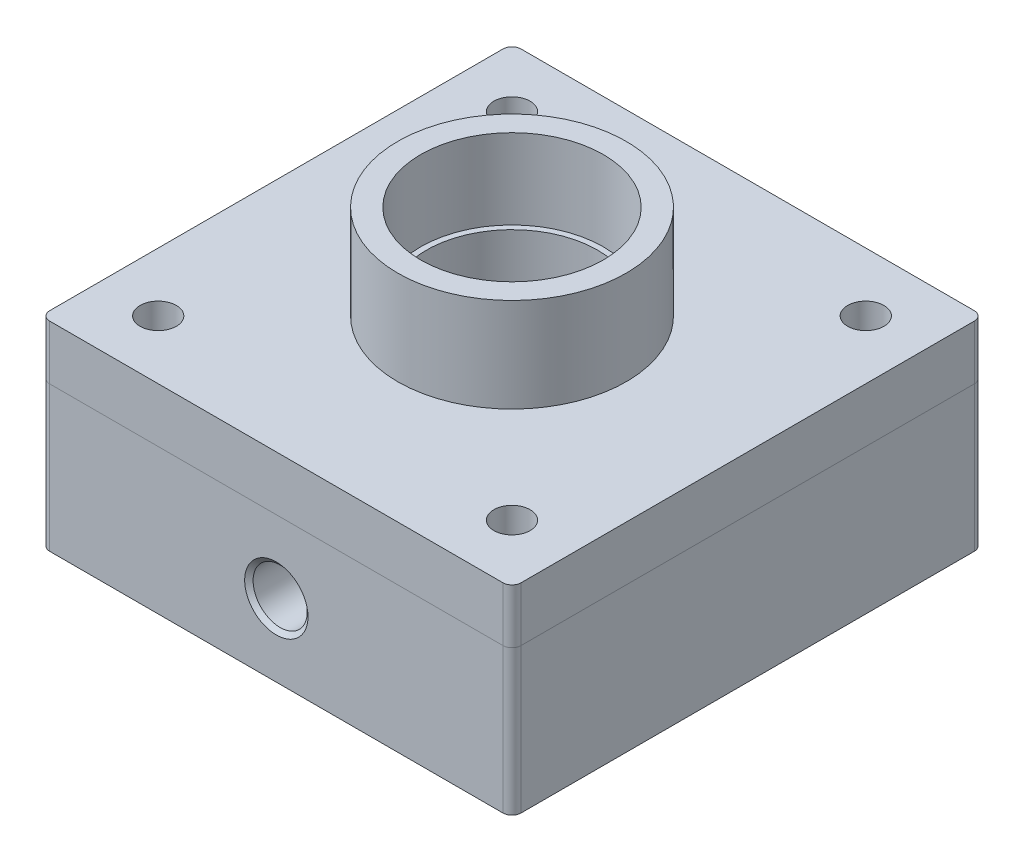
SolidWorks part; units mm, degrees
ref_plane "Front Plane" through (0, 0, 0) normal (0, 0, 1) x (1, 0, 0)
ref_plane "Top Plane" through (0, 0, 0) normal (0, 1, 0) x (1, 0, 0)
ref_plane "Right Plane" through (0, 0, 0) normal (1, 0, 0) x (0, 0, -1)
sketch "Sketch1" plane through (0, 0, 0) normal (0, 1, 0) x (1, 0, 0)
  line L1 (-82.55, 82.55) -> (82.55, 82.55)
  line L2 (-82.55, 82.55) -> (-82.55, -82.55)
  line L3 (-82.55, -82.55) -> (82.55, -82.55)
  line L4 (82.55, 82.55) -> (82.55, -82.55)
  line L5 (-82.55, 82.55) -> (82.55, -82.55) construction
  line L6 (-82.55, -82.55) -> (82.55, 82.55) construction
  point P0 (0, 0)
  dimension "D1" = 165.1
extrude "Boss-Extrude1" add sketch "Sketch1" along normal blind 50.8
sketch "Sketch2" plane through (0, 50.8, 0) normal (0, 1, 0) x (1, 0, 0)
  circle A0 centre (0, 0) radius 40
  dimension "D1" = 80
extrude "Boss-Extrude2" add sketch "Sketch2" along normal blind 52
sketch "Sketch3" plane through (0, 102.8, 0) normal (0, 1, 0) x (1, 0, 0)
  circle A0 centre (0, 0) radius 32
  dimension "D1" = 64
extrude "Cut-Extrude1" cut sketch "Sketch3" against normal blind 28
sketch "Sketch4" plane through (0, 74.8, 0) normal (0, 1, 0) x (1, 0, 0)
  circle A0 centre (0, 0) radius 30
  dimension "D1" = 60
extrude "Cut-Extrude2" cut sketch "Sketch4" against normal blind 22
fillet "Fillet1" radius 3.175 4 edges at (-82.55, 25.4, 82.55) (-82.55, 25.4, -82.55) (82.55, 25.4, -82.55) (82.55, 25.4, 82.55)
sketch "Sketch5" plane through (0, 0, 0) normal (0, -1, 0) x (1, 0, 0)
  circle A0 centre (0, 0) radius 20
  dimension "D1" = 40
extrude "Cut-Extrude3" cut sketch "Sketch5" against normal blind 40
sketch "Sketch6" plane through (0, 0, 0) normal (0, -1, 0) x (1, 0, 0)
  circle A0 centre (0, 0) radius 76.2
  circle A1 centre (0, 0) radius 69.85
  dimension "D1" = 152.4
  dimension "D2" = 139.7
extrude "Cut-Extrude4" cut sketch "Sketch6" against normal blind 8
sketch "Sketch7" plane through (0, 0, 82.55) normal (0, 0, 1) x (1, 0, 0)
  line L0 (-79.375, 25.4) -> (79.375, 25.4) construction
  line L1 (-79.375, 50.8) -> (-79.375, 0) construction
  line L2 (79.375, 0) -> (79.375, 50.8) construction
hole_wizard "1/2-14 NPSM Tapped Hole1" positions "Sketch8" profile "Sketch9" tap size "1/2-14 NPSM" standard "ANSI Inch"
sketch "Sketch8" plane through (0, 0, 82.55) normal (0, 0, 1) x (1, 0, 0)
  line L0 (-79.375, 25.4) -> (79.375, 25.4) construction
  point P0 (0, 25.4)
sketch "Sketch9" plane through (0, 25.4, 82.55) normal (1, 0, 0) x (0, -1, 0)
  line L0 (0, 0) -> (0, 52.9403)
  line L1 (0, 52.9403) -> (9.4869, 47.24)
  line L2 (9.4869, 47.24) -> (9.4869, 1.3427)
  line L3 (9.4869, 1.3427) -> (11.0871, 0)
  line L5 (11.0871, 0) -> (0, 0)
  line L6 (-9.4869, 1.3427) -> (-11.0871, 0) construction
  line L10 (0, 52.9403) -> (-9.4869, 47.24) construction
  line L11 (0, -6.35) -> (0, 107.95) construction
  dimension "Tap Drill Dia." = 18.9738
  dimension "Tap Drill Depth" = 47.24
  dimension "Near C'Sink Dia." = 22.1742
  dimension "Near C'Sink Angle" = 100
  dimension "Drill Angle" = 118
cosmetic thread "Hole Thread1" parameters "D1"=41.91, "D2"=20.9042
sketch "Sketch10" plane through (0, 0, 0) normal (0, -1, 0) x (1, 0, 0)
  line L0 (-79.375, 82.55) -> (79.375, 82.55) construction
  circle A0 centre (0, 50.55) radius 6.35
  dimension "D2" = 12.7
  dimension "D1" = 32
extrude "Cut-Extrude5" cut sketch "Sketch10" against normal blind 25
sketch "Sketch11" plane through (0, 0, 0) normal (0, -1, 0) x (1, 0, 0)
  line L1 (-61.9638, 61.9638) -> (61.9638, 61.9638) construction
  line L2 (-61.9638, 61.9638) -> (-61.9638, -61.9638) construction
  line L3 (-61.9638, -61.9638) -> (61.9638, -61.9638) construction
  line L4 (61.9638, 61.9638) -> (61.9638, -61.9638) construction
  line L5 (-61.9638, 61.9638) -> (61.9638, -61.9638) construction
  line L6 (-61.9638, -61.9638) -> (61.9638, 61.9638) construction
  circle A0 centre (0, 0) radius 87.63 construction
  circle A1 centre (-61.9638, 61.9638) radius 6.35
  circle A2 centre (61.9638, 61.9638) radius 6.35
  circle A3 centre (61.9638, -61.9638) radius 6.35
  circle A4 centre (-61.9638, -61.9638) radius 6.35
  dimension "D1" = 175.26
  dimension "D2" = 12.7
extrude "Cut-Extrude6" cut sketch "Sketch11" against normal through all
sketch "Sketch13" plane through (0, 50.8, 0) normal (0, 1, 0) x (1, 0, 0)
  line L4 (-82.55, 79.375) -> (-82.55, -79.375)
  line L5 (-79.375, -82.55) -> (79.375, -82.55)
  line L6 (82.55, -79.375) -> (82.55, 79.375)
  line L7 (79.375, 82.55) -> (-79.375, 82.55)
  line L8 (-82.55, 79.375) -> (-82.55, -79.375)
  line L9 (-79.375, -82.55) -> (79.375, -82.55)
  line L10 (82.55, -79.375) -> (82.55, 79.375)
  line L11 (79.375, 82.55) -> (-79.375, 82.55)
  circle A0 centre (61.9638, 61.9638) radius 6.35 construction
  circle A1 centre (61.9638, -61.9638) radius 6.35 construction
  circle A2 centre (0, 0) radius 40 construction
  circle A3 centre (-61.9638, -61.9638) radius 6.35 construction
  circle A4 centre (-61.9638, 61.9638) radius 6.35 construction
  circle A5 centre (61.9638, 61.9638) radius 6.35
  circle A6 centre (61.9638, -61.9638) radius 6.35
  circle A7 centre (0, 0) radius 40
  circle A8 centre (-61.9638, -61.9638) radius 6.35
  circle A9 centre (-61.9638, 61.9638) radius 6.35
  arc A14 (-82.55, -79.375) -> (-79.375, -82.55) centre (-79.375, -79.375) ccw
  arc A15 (79.375, -82.55) -> (82.55, -79.375) centre (79.375, -79.375) ccw
  arc A16 (82.55, 79.375) -> (79.375, 82.55) centre (79.375, 79.375) ccw
  arc A17 (-79.375, 82.55) -> (-82.55, 79.375) centre (-79.375, 79.375) ccw
  arc A18 (-82.55, -79.375) -> (-79.375, -82.55) centre (-79.375, -79.375) ccw
  arc A19 (79.375, -82.55) -> (82.55, -79.375) centre (79.375, -79.375) ccw
  arc A20 (82.55, 79.375) -> (79.375, 82.55) centre (79.375, 79.375) ccw
  arc A21 (-79.375, 82.55) -> (-82.55, 79.375) centre (-79.375, 79.375) ccw
  dimension "D1" = 0
extrude "Boss-Extrude3" add sketch "Sketch13" along normal blind 19.05 separate body
